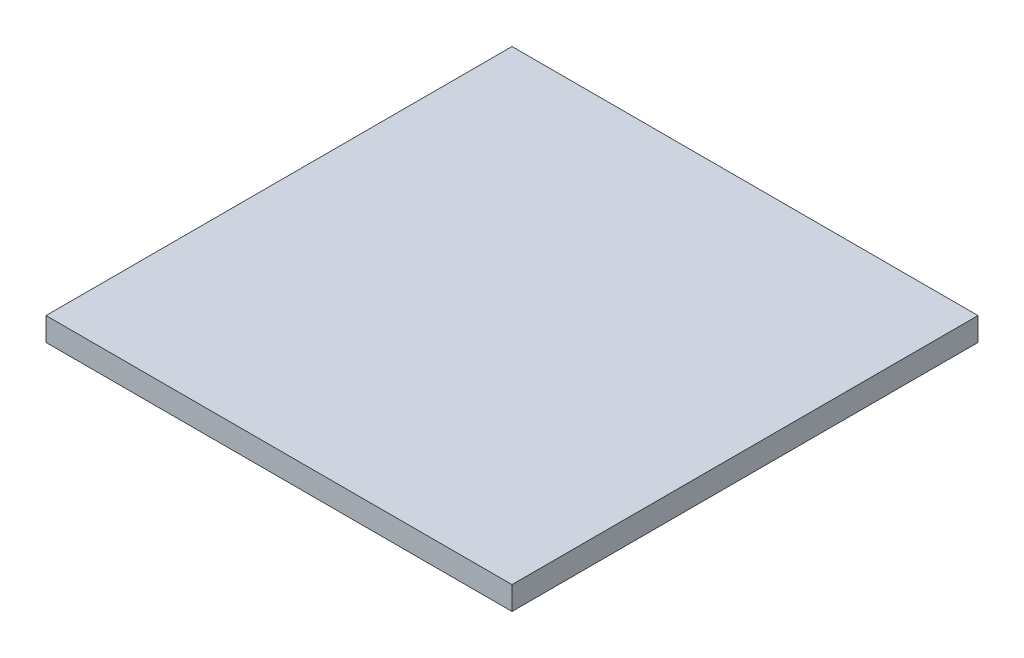
SolidWorks part; units mm, degrees
ref_plane "Front Plane" through (0, 0, 0) normal (0, 0, 1) x (1, 0, 0)
ref_plane "Top Plane" through (0, 0, 0) normal (0, 1, 0) x (1, 0, 0)
ref_plane "Right Plane" through (0, 0, 0) normal (1, 0, 0) x (0, 0, -1)
sketch "Sketch1" plane through (0, 0, 0) normal (0, 1, 0) x (1, 0, 0)
  line L1 (-196.9594, 0) -> (3.0406, 0)
  line L2 (-196.9594, 0) -> (-196.9594, -200)
  line L3 (-196.9594, -200) -> (3.0406, -200)
  line L4 (3.0406, 0) -> (3.0406, -200)
  dimension "D1" = 200
  dimension "D2" = 200
extrude "Boss-Extrude1" add sketch "Sketch1" along normal blind 10
